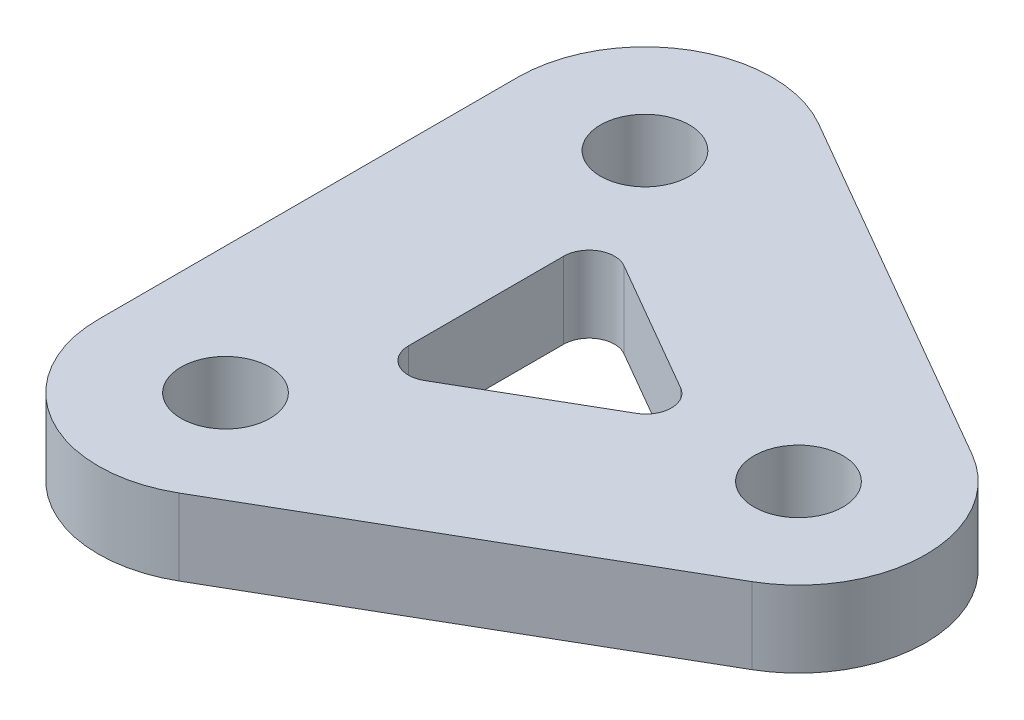
SolidWorks part; units mm, degrees
ref_plane "Front Plane" through (0, 0, 0) normal (0, 0, 1) x (1, 0, 0)
ref_plane "Top Plane" through (0, 0, 0) normal (0, 1, 0) x (1, 0, 0)
ref_plane "Right Plane" through (0, 0, 0) normal (1, 0, 0) x (0, 0, -1)
sketch "Sketch1" plane through (0, 0, 0) normal (0, 1, 0) x (1, 0, 0)
  line L1 (-10, -13) -> (10, -13)
  line L2 (-13, -10) -> (-13, 10)
  line L3 (-10, 13) -> (10, 13)
  line L4 (13, -10) -> (13, 10)
  line L5 (-13, -13) -> (13, 13) construction
  line L6 (-13, 13) -> (13, -13) construction
  line L7 (-7, -8) -> (7, -8)
  line L8 (-8, -7) -> (-8, 7)
  line L9 (-7, 8) -> (7, 8)
  line L10 (8, -7) -> (8, 7)
  line L11 (-8, -8) -> (8, 8) construction
  line L12 (-8, 8) -> (8, -8) construction
  circle A0 centre (-10, 10) radius 1.5
  circle A1 centre (10, 10) radius 1.5
  circle A2 centre (-10, -10) radius 1.5
  circle A3 centre (10, -10) radius 1.5
  arc A4 (-13, 10) -> (-10, 13) centre (-10, 10) cw
  arc A5 (13, 10) -> (10, 13) centre (10, 10) ccw
  arc A6 (-10, -13) -> (-13, -10) centre (-10, -10) cw
  arc A7 (13, -10) -> (10, -13) centre (10, -10) cw
  arc A8 (-8, 7) -> (-7, 8) centre (-7, 7) cw
  arc A9 (8, 7) -> (7, 8) centre (7, 7) ccw
  arc A10 (-7, -8) -> (-8, -7) centre (-7, -7) cw
  arc A11 (8, -7) -> (7, -8) centre (7, -7) cw
  point P0 (0, 0)
  point P31 (0, 0)
  dimension "D3" = 3
  dimension "D4" = 3
  dimension "D5" = 3
  dimension "D6" = 3
  dimension "D7" = 3
  dimension "D9" = 1
  dimension "D10" = 1
  dimension "D11" = 1
  dimension "D12" = 1
  dimension "D1" = 26
  dimension "D2" = 20
  dimension "D8" = 16
sketch "Sketch3" plane through (0, 0, 0) normal (0, 1, 0) x (1, 0, 0)
  line L0 (7.1447, 0) -> (-7.1447, 8.25) construction
  line L1 (-7.1447, 8.25) -> (-7.1447, -8.25) construction
  line L2 (-7.1447, -8.25) -> (7.1447, 0) construction
  line L3 (7.1447, 0) -> (-7.1447, 0) construction
  line L4 (9.6447, 4.3301) -> (-4.6447, 12.5801)
  line L5 (-12.1447, 8.25) -> (-12.1447, -8.25)
  line L6 (-4.6447, -12.5801) -> (9.6447, -4.3301)
  line L7 (17.1447, 0) -> (-12.1447, 16.9103) construction
  line L8 (-12.1447, 16.9103) -> (-12.1447, -16.9103) construction
  line L9 (-12.1447, -16.9103) -> (17.1447, 0) construction
  line L10 (1.6447, 0.866) -> (-3.6447, 3.9199)
  line L11 (-5.1447, 3.0538) -> (-5.1447, -3.0538)
  line L12 (-3.6447, -3.9199) -> (1.6447, -0.866)
  line L13 (-5.1447, -4.7859) -> (3.1447, 0) construction
  line L14 (3.1447, 0) -> (-5.1447, 4.7859) construction
  line L15 (-5.1447, 4.7859) -> (-5.1447, -4.7859) construction
  circle A0 centre (7.1447, 0) radius 1.75
  circle A1 centre (-7.1447, 8.25) radius 1.75
  circle A2 centre (-7.1447, -8.25) radius 1.75
  arc A3 (-4.6447, 12.5801) -> (-12.1447, 8.25) centre (-7.1447, 8.25) ccw
  arc A4 (-4.6447, -12.5801) -> (-12.1447, -8.25) centre (-7.1447, -8.25) cw
  arc A5 (9.6447, -4.3301) -> (9.6447, 4.3301) centre (7.1447, 0) ccw
  arc A6 (1.6447, -0.866) -> (1.6447, 0.866) centre (1.1447, 0) ccw
  arc A7 (-5.1447, -3.0538) -> (-3.6447, -3.9199) centre (-4.1447, -3.0538) ccw
  arc A8 (-5.1447, 3.0538) -> (-3.6447, 3.9199) centre (-4.1447, 3.0538) cw
  point P2 (0, 0)
  dimension "D4" = 3.5
  dimension "D6" = 5
  dimension "D7" = 5
  dimension "D9" = 1
  dimension "D1" = 60
  dimension "D2" = 60
  dimension "D3" = 16.5
  dimension "D5" = 5
  dimension "D8" = 2
extrude "Boss-Extrude1" add sketch "Sketch3" along normal blind 3
